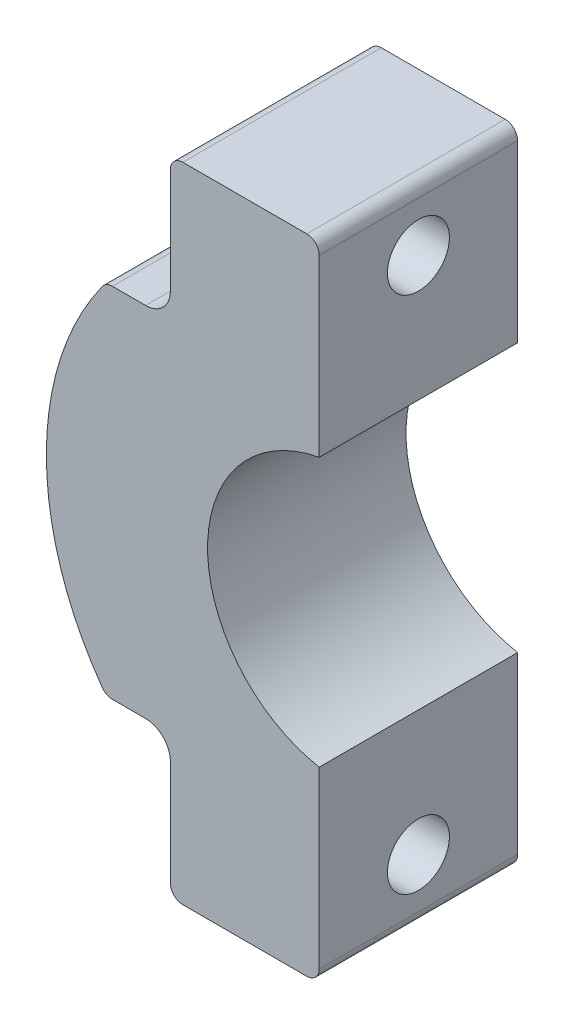
SolidWorks part; units mm, degrees
ref_plane "Plan de face" through (0, 0, 0) normal (0, 0, 1) x (1, 0, 0)
ref_plane "Plan de dessus" through (0, 0, 0) normal (0, 1, 0) x (1, 0, 0)
ref_plane "Plan de droite" through (0, 0, 0) normal (1, 0, 0) x (0, 0, -1)
sketch "Esquisse1" plane through (0, 0, 0) normal (0, 0, 1) x (1, 0, 0)
  circle A0 centre (0, 0) radius 13
  circle A1 centre (0, 0) radius 5.5
  dimension "D1" = 11
  dimension "D2" = 26
extrude "Boss.-Extru.1" add sketch "Esquisse1" along normal blind 8
sketch "Esquisse2" plane through (0, 0, 8) normal (0, 0, 1) x (1, 0, 0)
  line L1 (-1, 24.2432) -> (31.31, 24.2432)
  line L2 (-1, 24.2432) -> (-1, -25.575)
  line L3 (-1, -25.575) -> (31.31, -25.575)
  line L4 (31.31, 24.2432) -> (31.31, -25.575)
  dimension "D1" = 1
extrude "Enlèv. mat.-Extru.1" cut sketch "Esquisse2" against normal blind 8
sketch "Esquisse3" plane through (-1, 0, 0) normal (1, 0, 0) x (0, 0, -1)
  line L0 (-8, 12.9615) -> (-8, 5.4083) construction
  line L1 (-8, 12.9615) -> (0, 12.9615) construction
  line L2 (0, -12.9615) -> (-8, -12.9615) construction
  line L4 (-8, -5.4083) -> (-8, -12.9615) construction
  circle A0 centre (-4, 10.4615) radius 1.5
  circle A1 centre (-4, -10.4615) radius 1.5
  dimension "D1" = 3
  dimension "D4" = 3
  dimension "D2" = 4
  dimension "D3" = 2.5
  dimension "D5" = 2.5
  dimension "D6" = 4
extrude "Enlèv. mat.-Extru.2" cut sketch "Esquisse3" against normal blind 8
sketch "Esquisse4" plane through (0, 0, 8) normal (0, 0, 1) x (1, 0, 0)
  line L0 (-9, 8.9615) -> (-1, 8.9615) construction
  line L1 (-28.8712, 21.0445) -> (-7, 21.0445)
  line L2 (-28.8712, 21.0445) -> (-28.8712, 7.2115)
  line L3 (-28.8712, 7.2115) -> (-7, 7.2115)
  line L4 (-7, 21.0445) -> (-7, 7.2115)
  line L5 (-1, 12.9615) -> (-1, 5.4083) construction
  line L6 (-1, -5.4083) -> (-1, -12.9615) construction
  line L7 (-7, -7.2115) -> (-27.4321, -7.2115)
  line L8 (-7, -7.2115) -> (-7, -17.5209)
  line L9 (-7, -17.5209) -> (-27.4321, -17.5209)
  line L10 (-27.4321, -7.2115) -> (-27.4321, -17.5209)
  line L11 (-1, -8.9615) -> (-9, -8.9615) construction
  dimension "D1" = 1.75
  dimension "D2" = 6
  dimension "D3" = 6
  dimension "D4" = 1.75
extrude "Enlèv. mat.-Extru.3" cut sketch "Esquisse4" against normal blind 8
sketch "Esquisse6" plane through (0, 0, 8) normal (0, 0, 1) x (1, 0, 0)
  line L0 (-16.7336, -12.2449) -> (-8.1777, -8.7821)
  line L1 (-13.1779, 8.6969) -> (-7.7945, 9.1239)
  arc A0 (-7.7945, 9.1239) -> (-8.1777, -8.7821) centre (0, 0) ccw
  arc A1 (-13.1779, 8.6969) -> (-16.7336, -12.2449) centre (-5.9631, -3.3009) ccw
  dimension "D1" = 12
  dimension "D2" = 14
extrude "Enlèv. mat.-Extru.4" cut sketch "Esquisse6" against normal blind 8
fillet "Congé4" radius 0.5 2 edges at (-9.5914, -7.2115, 4) (-9.5914, 7.2115, 4)
sketch "Esquisse7" plane through (0, 0, 0) normal (0, 0, -1) x (-1, 0, 0)
  line L1 (7, 7.2115) -> (1, 7.2115)
  line L2 (7, 7.2115) -> (7, 12.9615)
  line L3 (7, 12.9615) -> (1, 12.9615)
  line L4 (1, 7.2115) -> (1, 12.9615)
  line L5 (7, -7.2115) -> (1, -7.2115)
  line L6 (7, -7.2115) -> (7, -12.9615)
  line L7 (7, -12.9615) -> (1, -12.9615)
  line L8 (1, -7.2115) -> (1, -12.9615)
extrude "Boss.-Extru.3" add sketch "Esquisse7" against normal blind 8
sketch "Esquisse11" plane through (-1, 0, 0) normal (1, 0, 0) x (0, 0, -1)
  line L0 (-8, 12.9615) -> (-8, 5.4083) construction
  line L1 (-8, -5.4083) -> (-8, -12.9615) construction
  line L2 (-8, 12.9615) -> (0, 12.9615) construction
  line L3 (0, -12.9615) -> (-8, -12.9615) construction
  circle A0 centre (-4, 10.4615) radius 1.25
  circle A1 centre (-4, -10.4615) radius 1.25
  dimension "D1" = 4
  dimension "D5" = 2.5
  dimension "D6" = 2.5
  dimension "D2" = 4
  dimension "D3" = 2.5
  dimension "D4" = 2.5
extrude "Enlèv. mat.-Extru.5" cut sketch "Esquisse11" against normal blind 8 contours A0
fillet "Congé5" radius 0.5 2 edges at (-7, -12.9615, 4) (-7, 12.9615, 4)
fillet "Congé6" radius 1 2 edges at (-7, -7.2115, 4) (-7, 7.2115, 4)
fillet "Congé7" radius 0.5 2 edges at (-1, -12.9615, 4) (-1, 12.9615, 4)
